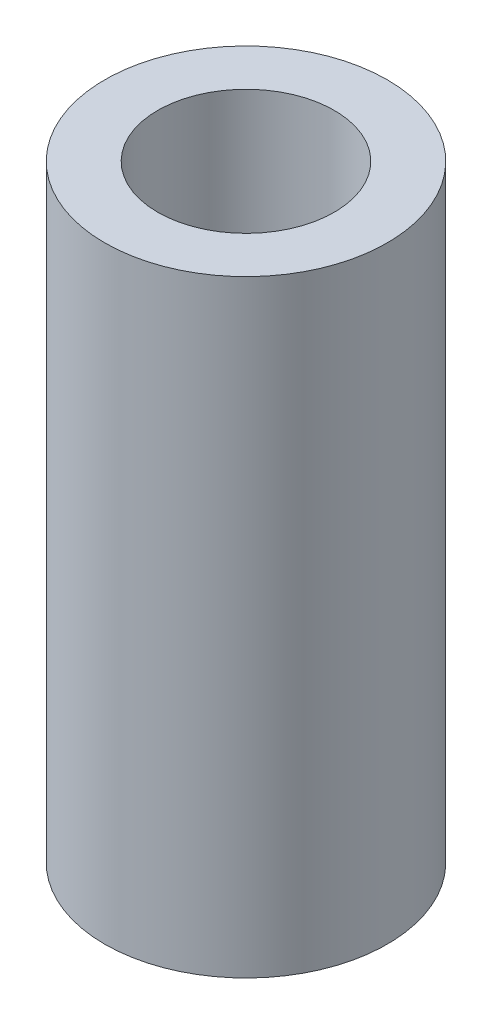
SolidWorks part; units mm, degrees
ref_plane "Front Plane" through (0, 0, 0) normal (0, 0, 1) x (1, 0, 0)
ref_plane "Top Plane" through (0, 0, 0) normal (0, 1, 0) x (1, 0, 0)
ref_plane "Right Plane" through (0, 0, 0) normal (1, 0, 0) x (0, 0, -1)
sketch "Sketch1" plane through (0, 0, 0) normal (0, 1, 0) x (1, 0, 0)
  circle A0 centre (0, 0) radius 2.5
  circle A1 centre (0, 0) radius 4
  dimension "D1" = 5
  dimension "D2" = 1.5
extrude "Boss-Extrude1" add sketch "Sketch1" along normal blind 17.2
